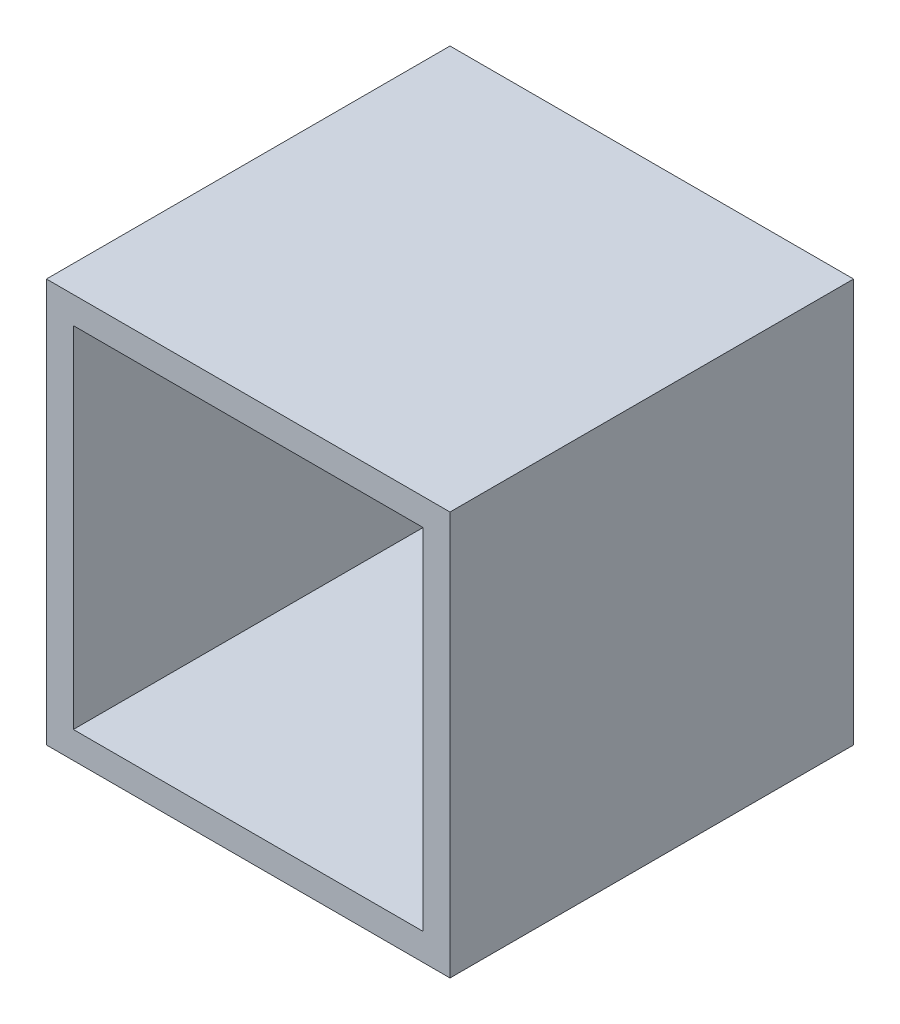
SolidWorks part; units mm, degrees
ref_plane "Front Plane" through (0, 0, 0) normal (0, 0, 1) x (1, 0, 0)
ref_plane "Top Plane" through (0, 0, 0) normal (0, 1, 0) x (1, 0, 0)
ref_plane "Right Plane" through (0, 0, 0) normal (1, 0, 0) x (0, 0, -1)
sketch "Sketch1" plane through (0, 0, 0) normal (0, 0, 1) x (1, 0, 0)
  line L1 (-44.3454, 128.9567) -> (105.6546, 128.9567)
  line L2 (-44.3454, 128.9567) -> (-44.3454, -21.0433)
  line L3 (-44.3454, -21.0433) -> (105.6546, -21.0433)
  line L4 (105.6546, 128.9567) -> (105.6546, -21.0433)
extrude "Boss-Extrude1" add sketch "Sketch1" along normal blind 150
sketch "Sketch3" plane through (0, 0, 150) normal (0, 0, 1) x (1, 0, 0)
  line L8 (-34.3454, 118.9567) -> (-34.3454, -11.0433)
  line L9 (-34.3454, -11.0433) -> (95.6546, -11.0433)
  line L10 (95.6546, -11.0433) -> (95.6546, 118.9567)
  line L11 (95.6546, 118.9567) -> (-34.3454, 118.9567)
  line L12 (-34.3454, 118.9567) -> (-34.3454, -11.0433)
  line L13 (-34.3454, -11.0433) -> (95.6546, -11.0433)
  line L14 (95.6546, -11.0433) -> (95.6546, 118.9567)
  line L15 (95.6546, 118.9567) -> (-34.3454, 118.9567)
  dimension "D1" = 10
extrude "Cut-Extrude1" cut sketch "Sketch3" against normal blind 140
